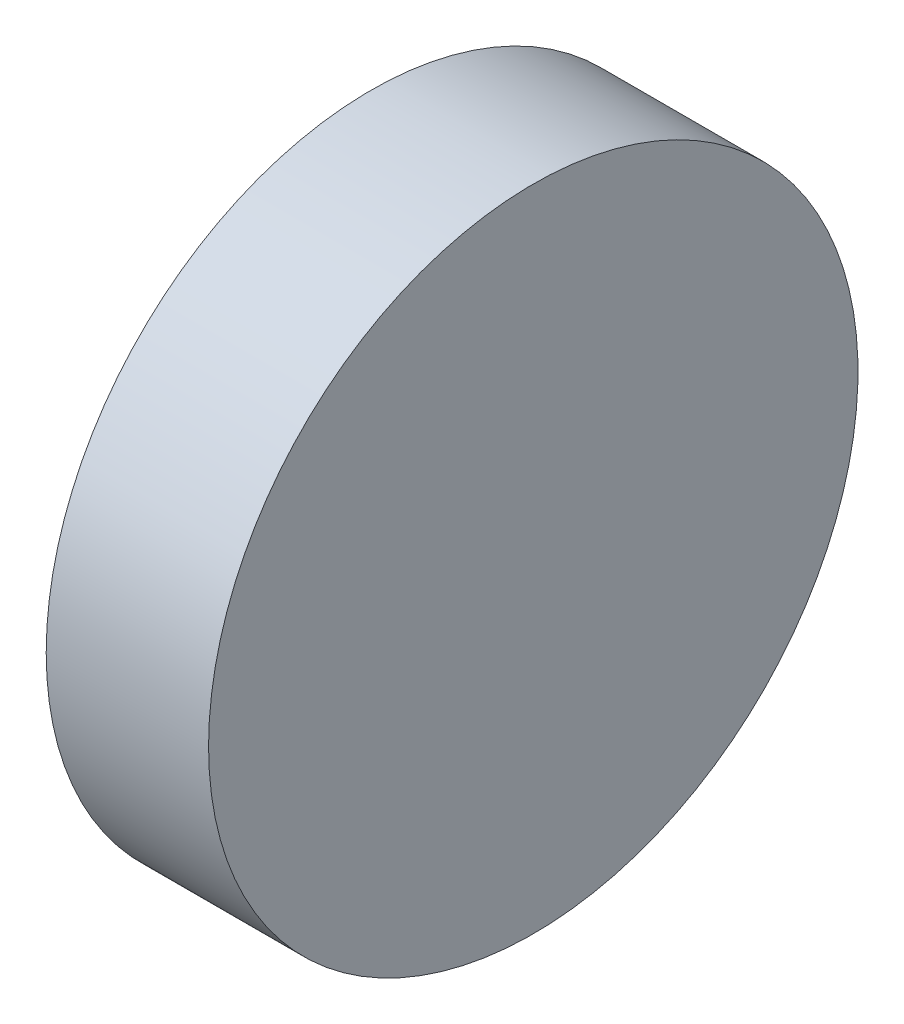
SolidWorks part; units mm, degrees
ref_plane "前视基准面" through (0, 0, 0) normal (0, 0, 1) x (1, 0, 0)
ref_plane "上视基准面" through (0, 0, 0) normal (0, 1, 0) x (1, 0, 0)
ref_plane "右视基准面" through (0, 0, 0) normal (1, 0, 0) x (0, 0, -1)
sketch "草图1" plane through (0, 0, 0) normal (0, 0, 1) x (1, 0, 0)
  line L0 (254.0008, 77.2932) -> (276.4386, 77.2932) construction
  line L1 (259.7244, 77.2932) -> (259.7244, 89.9932)
  line L2 (259.7244, 89.9932) -> (266.0744, 89.9932)
  line L3 (266.0744, 89.9932) -> (266.0744, 77.2932)
  line L4 (266.0744, 77.2932) -> (259.7244, 77.2932)
  dimension "D1" = 6.35
revolve "旋转1" add sketch "草图1" angle 360 about L0
